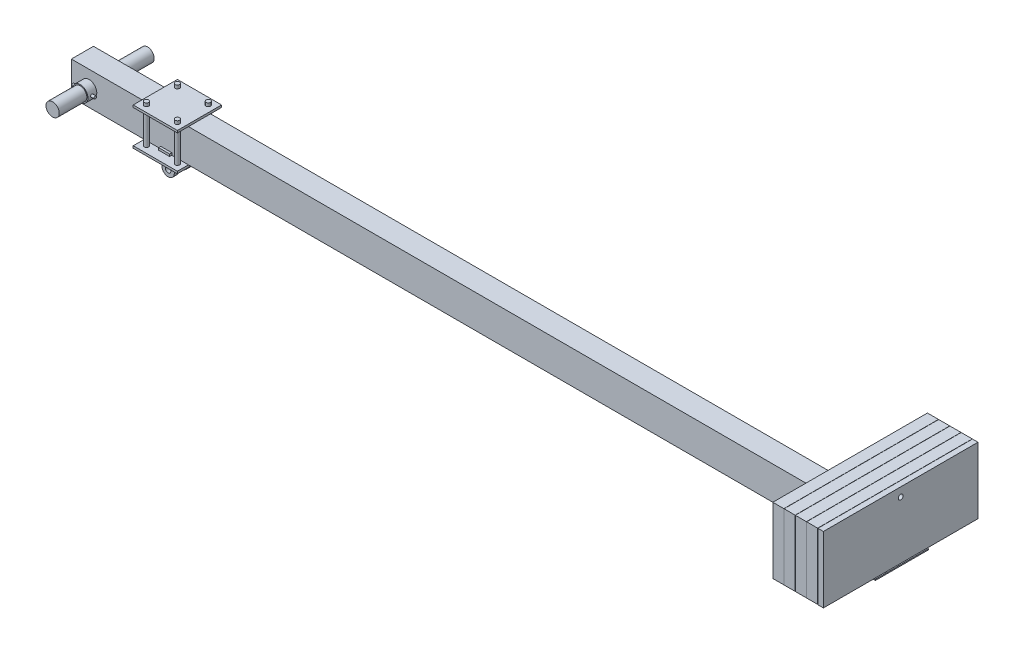
SolidWorks part; units mm, degrees
material "Plain Carbon Steel"
ref_plane "Front Plane" through (0, 0, 0) normal (0, 0, 1) x (1, 0, 0)
ref_plane "Top Plane" through (0, 0, 0) normal (0, 1, 0) x (1, 0, 0)
ref_plane "Right Plane" through (0, 0, 0) normal (1, 0, 0) x (0, 0, -1)
sketch "Sketch1" plane through (0, 0, 0) normal (0, 0, 1) x (1, 0, 0)
  line L0 (3600, 0) -> (0, 0) construction
  line L1 (0, -75) -> (3600, -75)
  line L2 (0, -75) -> (0, 75) construction
  line L3 (0, 75) -> (3600, 75)
  line L4 (3600, -75) -> (3600, 75) construction
  line L5 (3600, 225) -> (3600, -75) construction
  line L6 (3600, 75) -> (3600, 225)
  line L7 (3600, 225) -> (3650, 225)
  line L8 (3650, 225) -> (3650, -75)
  line L9 (3650, -75) -> (3600, -75)
  line L11 (3650, 225) -> (3651, 225) construction
  line L26 (0, 75) -> (-80, 75)
  line L27 (-80, 75) -> (-80, -75)
  line L28 (-80, -75) -> (0, -75)
  dimension "D1" = 3600
  dimension "D2" = 150
  dimension "D3" = 300
  dimension "D4" = 50
  dimension "D6" = 80
extrude "Boss-Extrude1" add sketch "Sketch1" along normal mid plane 100
sketch "Sketch2" plane through (0, 0, 0) normal (0, 0, 1) x (1, 0, 0)
  line L0 (-74, 0) -> (3600, 0) construction
  line L1 (-74, -69) -> (3600, -69)
  line L2 (-74, -69) -> (-74, 69)
  line L3 (-74, 69) -> (3600, 69)
  line L4 (3600, -69) -> (3600, 69)
  line L5 (3600, 75) -> (-80, 75) construction
  line L8 (3600, 225) -> (3600, 75) construction
  line L9 (-80, 75) -> (-80, -75) construction
  dimension "D1" = 6
  dimension "D2" = 6
extrude "Cut-Extrude1" cut sketch "Sketch2" against normal mid plane 88
sketch "Sketch3" plane through (0, 0, 0) normal (0, 0, 1) x (1, 0, 0)
  line L24 (3600, 225) -> (3600, 75) construction
  line L25 (3650, 225) -> (3600, 225) construction
  line L26 (3650, -75) -> (3650, 225) construction
  line L27 (-80, -75) -> (3650, -75) construction
  line L28 (3600, 225) -> (3600, -75)
  line L29 (3650, 225) -> (3600, 225)
  line L30 (3650, -75) -> (3650, 225)
  line L31 (3600, -75) -> (3650, -75)
extrude "Boss-Extrude2" add sketch "Sketch3" along normal mid plane 700
sketch "Sketch6" plane through (0, 0, 0) normal (0, 0, 1) x (1, 0, 0)
  line L0 (3600, 75) -> (-80, 75) construction
  line L1 (250, 75) -> (450, 75)
  line L2 (250, 75) -> (250, 85)
  line L3 (250, 85) -> (450, 85)
  line L4 (450, 75) -> (450, 85)
  line L5 (-80, -75) -> (3600, -75) construction
  line L6 (250, -75) -> (450, -75)
  line L7 (250, -75) -> (250, -85)
  line L8 (250, -85) -> (450, -85)
  line L9 (450, -75) -> (450, -85)
  line L10 (350, 85) -> (350, 75) construction
  dimension "D1" = 200
  dimension "D2" = 10
  dimension "D3" = 350
extrude "Boss-Extrude4" add sketch "Sketch6" along normal mid plane 200
sketch "Sketch14" plane through (0, 0, 0) normal (0, 0, 1) x (1, 0, 0)
  circle A0 centre (0, 0) radius 35
  dimension "D1" = 70
extrude "Cut-Extrude5" cut sketch "Sketch14" against normal mid plane 192
sketch "Sketch15" plane through (0, 0, 0) normal (0, 0, 1) x (1, 0, 0)
  circle A0 centre (0, 0) radius 30
  circle A1 centre (0, 0) radius 35
  dimension "D1" = 70
  dimension "D2" = 60
extrude "Boss-Extrude9" add sketch "Sketch15" along normal mid plane 180
sketch "Sketch8" plane through (0, 0, 0) normal (0, 0, 1) x (1, 0, 0)
  circle A0 centre (0, 0) radius 30
  dimension "D1" = 60
extrude "Boss-Extrude6" add sketch "Sketch8" along normal mid plane 430
sketch "Sketch9" plane through (0, 0, 0) normal (0, 0, 1) x (1, 0, 0)
  line L0 (250, -85) -> (450, -85) construction
  line L1 (250, -85) -> (450, -85) construction
  line L2 (350, -85) -> (350, 31.3926) construction
  line L3 (295, -85) -> (295, -110)
  line L4 (295, -110) -> (405, -110) construction
  line L5 (405, -85) -> (405, -110)
  line L6 (350, -110) -> (350, -309.6124) construction
  line L7 (378, -110) -> (378, -148)
  line L8 (322, -110) -> (322, -148)
  line L9 (295, -110) -> (322, -110)
  line L10 (378, -110) -> (405, -110)
  line L11 (295, -85) -> (405, -85)
  arc A0 (378, -148) -> (322, -148) centre (350, -148) cw
  circle A1 centre (350, -148) radius 12.5
  dimension "D3" = 28
  dimension "D4" = 25
  dimension "D1" = 25
  dimension "D2" = 110
  dimension "D5" = 38
extrude "Boss-Extrude7" add sketch "Sketch9" along normal mid plane 84
sketch "Sketch10" plane through (322, 0, 0) normal (-1, 0, 0) x (0, 0, 1)
  line L1 (-20, -85) -> (20, -85)
  line L2 (-20, -85) -> (-20, -176)
  line L3 (-20, -176) -> (20, -176)
  line L4 (20, -85) -> (20, -176)
  line L5 (-42, -176) -> (42, -176) construction
  line L6 (42, -85) -> (-42, -85) construction
  line L7 (-42, -129) -> (-20, -129) construction
  line L8 (-42, -110) -> (-42, -148) construction
  line L9 (20, -129) -> (42, -129) construction
  line L10 (42, -110) -> (42, -148) construction
  dimension "D1" = 40
extrude "Cut-Extrude3" cut sketch "Sketch10" against normal blind 170 and the other way blind 84
sketch "Sketch11" plane through (0, 0, 0) normal (0, 1, 0) x (1, 0, 0)
  line L0 (280, -70) -> (420, -70) construction
  line L1 (280, -70) -> (280, 70) construction
  line L2 (420, -70) -> (420, 70) construction
  line L3 (280, 70) -> (420, 70) construction
  line L4 (280, -70) -> (420, 70) construction
  line L5 (420, -70) -> (280, 70) construction
  line L6 (250, -100) -> (250, 100) construction
  line L7 (450, 100) -> (250, 100) construction
  line L8 (280, 0) -> (250, 0) construction
  line L9 (420, 0) -> (450, 0) construction
  line L10 (450, -100) -> (450, 100) construction
  circle A0 centre (420, 70) radius 10
  circle A1 centre (420, -70) radius 10
  circle A2 centre (280, -70) radius 10
  circle A3 centre (280, 70) radius 10
  point P1 (350, 0)
  dimension "D3" = 20
  dimension "D1" = 30
  dimension "D2" = 30
extrude "Boss-Extrude8" add sketch "Sketch11" along normal blind 100 and the other way blind 100
sketch "Sketch24" plane through (0, 75, 0) normal (0, 1, 0) x (1, 0, 0)
  line L0 (250, -50) -> (450, -50) construction
  line L1 (250, -50) -> (450, -50) construction
  line L2 (350, -50) -> (350, -158.2957) construction
  line L3 (325, -50) -> (375, -50)
  line L4 (325, -50) -> (325, -60)
  line L5 (325, -60) -> (375, -60)
  line L6 (375, -50) -> (375, -60)
  line L7 (0, 0) -> (647.6373, 0) construction
  line L8 (375, 50) -> (375, 60)
  line L9 (325, 60) -> (375, 60)
  line L10 (325, 50) -> (325, 60)
  line L11 (325, 50) -> (375, 50)
  point P8 (350, -50)
  point P9 (350, -60)
  dimension "D1" = 10
  dimension "D2" = 50
extrude "Boss-Extrude15" add sketch "Sketch24" against normal blind 10
sketch "Sketch25" plane through (0, -75, 0) normal (0, 1, 0) x (1, 0, 0)
  line L8 (325, -60) -> (325, -50) construction
  line L9 (325, -50) -> (375, -50) construction
  line L10 (375, -50) -> (375, -60) construction
  line L11 (375, -60) -> (325, -60) construction
  line L12 (375, 50) -> (325, 50) construction
  line L13 (325, 50) -> (325, 60) construction
  line L14 (325, 60) -> (375, 60) construction
  line L15 (375, 60) -> (375, 50) construction
  line L16 (325, -60) -> (325, -50)
  line L17 (325, -50) -> (375, -50)
  line L18 (375, -50) -> (375, -60)
  line L19 (375, -60) -> (325, -60)
  line L20 (375, 50) -> (325, 50)
  line L21 (325, 50) -> (325, 60)
  line L22 (325, 60) -> (375, 60)
  line L23 (375, 60) -> (375, 50)
extrude "Boss-Extrude16" add sketch "Sketch25" along normal blind 10
sketch "Sketch16" plane through (0, -75, 0) normal (0, -1, 0) x (1, 0, 0)
  line L0 (3250, -120) -> (3630, -120)
  line L1 (3250, -120) -> (3250, 120)
  line L2 (3630, -120) -> (3630, 120)
  line L3 (3250, 120) -> (3630, 120)
  line L4 (3250, -120) -> (3630, 120) construction
  line L5 (3630, -120) -> (3250, 120) construction
  line L6 (3650, 350) -> (3650, -350) construction
  line L7 (450, 50) -> (3600, 50) construction
  line L8 (450, -50) -> (3600, -50) construction
  line L9 (3600, 350) -> (3600, 50) construction
  point P1 (3440, 0)
  dimension "D1" = 20
  dimension "D2" = 70
  dimension "D3" = 70
  dimension "D4" = 350
extrude "Boss-Extrude10" add sketch "Sketch16" along normal blind 5
sketch "Sketch17" plane through (3600, 0, 0) normal (-1, 0, 0) x (0, 0, 1)
  line L0 (-350, 225) -> (-350, -75) construction
  line L2 (350, 225) -> (-350, 225) construction
  line B0 (0, -6.4214) -> (0, 225) construction
  line B1 (0, -6.4214) -> (319.7322, -6.4214) construction
  line B2 (350, 225) -> (-350, 225)
  line B3 (-350, 225) -> (-350, -74)
  line B4 (-350, -74) -> (-65, -74)
  line B5 (-65, -74) -> (-55, -64)
  line B6 (-55, 75.1) -> (55, 75.1)
  line B7 (-55, -64) -> (-55, 75.1)
  line B8 (55, -64) -> (55, 75.1)
  line B9 (65, -74) -> (55, -64)
  line B10 (350, -74) -> (65, -74)
  line B11 (350, 225) -> (350, -74)
sketch_block_instance "Block1-1"
sketch_block "Block1" parameters "D1"=135, "D2"=10, "D3"=230, "D4"=230, "D5"=285
extrude "Boss-Extrude11" add sketch "Sketch17" along normal blind 50 from offset 1 separate body
sketch "Sketch18" plane through (3549, 0, 0) normal (-1, 0, 0) x (0, 0, 1)
  line L0 (350, -74) -> (350, 225) construction
  line L1 (350, 225) -> (-350, 225) construction
  line B0 (350, 225) -> (-350, 225)
  line B1 (-350, 225) -> (-350, -74)
  line B2 (-350, -74) -> (-65, -74)
  line B3 (-65, -74) -> (-55, -64)
  line B4 (-55, 75.1) -> (55, 75.1)
  line B5 (-55, -64) -> (-55, 75.1)
  line B6 (55, -64) -> (55, 75.1)
  line B7 (65, -74) -> (55, -64)
  line B8 (350, -74) -> (65, -74)
  line B9 (350, 225) -> (350, -74)
sketch_block_instance "Block1-2"
extrude "Boss-Extrude12" add sketch "Sketch18" along normal blind 50 from offset 1 separate body
sketch "Sketch19" plane through (3498, 0, 0) normal (-1, 0, 0) x (0, 0, 1)
  line L0 (-350, 225) -> (-350, -74) construction
  line L1 (350, 225) -> (-350, 225) construction
  line B0 (350, 225) -> (-350, 225)
  line B1 (-350, 225) -> (-350, -74)
  line B2 (-350, -74) -> (-65, -74)
  line B3 (-65, -74) -> (-55, -64)
  line B4 (-55, 75.1) -> (55, 75.1)
  line B5 (-55, -64) -> (-55, 75.1)
  line B6 (55, -64) -> (55, 75.1)
  line B7 (65, -74) -> (55, -64)
  line B8 (350, -74) -> (65, -74)
  line B9 (350, 225) -> (350, -74)
sketch_block_instance "Block1-4"
extrude "Boss-Extrude13" add sketch "Sketch19" along normal blind 50 from offset 1 separate body
sketch "Sketch20" plane through (3447, 0, 0) normal (-1, 0, 0) x (0, 0, 1)
  line L0 (350, 225) -> (-350, 225) construction
  line L1 (350, -74) -> (350, 225) construction
  line B0 (350, 225) -> (-350, 225)
  line B1 (-350, 225) -> (-350, -74)
  line B2 (-350, -74) -> (-65, -74)
  line B3 (-65, -74) -> (-55, -64)
  line B4 (-55, 75.1) -> (55, 75.1)
  line B5 (-55, -64) -> (-55, 75.1)
  line B6 (55, -64) -> (55, 75.1)
  line B7 (65, -74) -> (55, -64)
  line B8 (350, -74) -> (65, -74)
  line B9 (350, 225) -> (350, -74)
sketch_block_instance "Block1-6"
extrude "Boss-Extrude14" add sketch "Sketch20" along normal blind 50 from offset 1 separate body
sketch "Sketch21" plane through (0, -80, 0) normal (0, -1, 0) x (1, 0, 0)
  line L0 (3250, 0) -> (3630, 0) construction
  line L1 (3630, -120) -> (3630, 120) construction
  line L2 (3250, 50) -> (3250, -50) construction
  line L3 (3290, 80) -> (3590, 80) construction
  line L4 (3290, 89) -> (3590, 89)
  line L5 (3290, 71) -> (3590, 71)
  line L6 (3650, 350) -> (3650, -350) construction
  line L7 (3250, 120) -> (3250, -120) construction
  line L8 (3290, -80) -> (3590, -80) construction
  line L9 (3290, -89) -> (3590, -89)
  line L10 (3290, -71) -> (3590, -71)
  arc A0 (3290, 89) -> (3290, 71) centre (3290, 80) ccw
  arc A1 (3590, 71) -> (3590, 89) centre (3590, 80) ccw
  arc A2 (3290, -89) -> (3290, -71) centre (3290, -80) cw
  arc A3 (3590, -71) -> (3590, -89) centre (3590, -80) cw
  point P8 (3440, 80)
  point P19 (3440, -80)
  dimension "D1" = 18
  dimension "D2" = 60
  dimension "D3" = 40
  dimension "D4" = 80
extrude "Cut-Extrude6" cut sketch "Sketch21" against normal up to surface (5 mm away) up to face at (3425, -75, 85)
sketch "Sketch22" plane through (0, -80, 0) normal (0, -1, 0) x (1, 0, 0)
  line L0 (3421, 350) -> (3421, -350) construction
  line L1 (3396, 350) -> (3446, 350) construction
  line L2 (3396, -350) -> (3446, -350) construction
  line L3 (3472, -350) -> (3472, 350) construction
  line L4 (3447, -350) -> (3497, -350) construction
  line L5 (3447, 350) -> (3497, 350) construction
  line L6 (3523, 350) -> (3523, -350) construction
  line L7 (3498, 350) -> (3548, 350) construction
  line L8 (3498, -350) -> (3548, -350) construction
  line L9 (3574, -350) -> (3574, 350) construction
  line L10 (3549, -350) -> (3599, -350) construction
  line L11 (3549, 350) -> (3599, 350) construction
  line L12 (3421, 80) -> (3574, 80) construction
  line L13 (3250, 0) -> (3630, 0) construction
  line L14 (3630, -120) -> (3630, 120) construction
  line L15 (3250, 120) -> (3250, -120) construction
  circle A0 centre (3421, 80) radius 8
  circle A1 centre (3472, 80) radius 8
  circle A2 centre (3523, 80) radius 8
  circle A3 centre (3574, 80) radius 8
  circle A4 centre (3574, -80) radius 8
  circle A5 centre (3523, -80) radius 8
  circle A6 centre (3472, -80) radius 8
  circle A7 centre (3421, -80) radius 8
  dimension "D2" = 16
  dimension "D1" = 80
extrude "Cut-Extrude7" cut sketch "Sketch22" against normal blind 30
sketch "Sketch23" plane through (3650, 0, 0) normal (1, 0, 0) x (0, 0, -1)
  line L0 (0, 0) -> (0, 225) construction
  line L1 (-350, 225) -> (350, 225) construction
  circle A0 centre (0, 185) radius 11
  dimension "D2" = 22
  dimension "D1" = 40
extrude "Cut-Extrude8" cut sketch "Sketch23" against normal up to surface (254 mm away) up to face at (3396, 17.62, 0)
sketch "Sketch26" plane through (3396, 0, 0) normal (-1, 0, 0) x (0, 0, 1)
  line L10 (-350, 225) -> (-350, -74)
  line L11 (-350, -74) -> (-65, -74)
  line L12 (-65, -74) -> (-55, -64)
  line L13 (-55, -64) -> (-55, 75.1)
  line L14 (-55, 75.1) -> (55, 75.1)
  line L15 (55, 75.1) -> (55, -64)
  line L16 (55, -64) -> (65, -74)
  line L17 (65, -74) -> (350, -74)
  line L18 (350, -74) -> (350, 225)
  line L19 (350, 225) -> (-350, 225)
  line L20 (-350, 225) -> (-350, -74)
  line L21 (-350, -74) -> (-65, -74)
  line L22 (-65, -74) -> (-55, -64)
  line L23 (-55, -64) -> (-55, 75.1)
  line L24 (-55, 75.1) -> (55, 75.1)
  line L25 (55, 75.1) -> (55, -64)
  line L26 (55, -64) -> (65, -74)
  line L27 (65, -74) -> (350, -74)
  line L28 (350, -74) -> (350, 225)
  line L29 (350, 225) -> (-350, 225)
  dimension "D1" = 0
extrude "Cut-Extrude9" [suppressed] cut sketch "Sketch26" against normal up to surface (204 mm away)
sketch "Sketch27" plane through (0, 75, 0) normal (0, 1, 0) x (1, 0, 0)
  line L0 (3600, 50) -> (450, 50) construction
  line L1 (3599.2561, 50) -> (3547.973, 50)
  line L2 (3599.2561, 50) -> (3599.2561, -50)
  line L3 (3599.2561, -50) -> (3547.973, -50)
  line L4 (3547.973, 50) -> (3547.973, -50)
  line L5 (3600, -50) -> (450, -50) construction
  line L7 (3546.5878, 50) -> (3497.0658, 50)
  line L8 (3546.5878, 50) -> (3546.5878, -50)
  line L9 (3546.5878, -50) -> (3497.0658, -50)
  line L10 (3497.0658, 50) -> (3497.0658, -50)
  line L11 (3495.8537, 50) -> (3446.0845, 50)
  line L12 (3495.8537, 50) -> (3495.8537, -50)
  line L13 (3495.8537, -50) -> (3446.0845, -50)
  line L14 (3446.0845, 50) -> (3446.0845, -50)
  line L15 (3444.8877, 50) -> (3395.1343, 50)
  line L16 (3444.8877, 50) -> (3444.8877, -50)
  line L17 (3444.8877, -50) -> (3395.1343, -50)
  line L18 (3395.1343, 50) -> (3395.1343, -50)
split line "Split Line1" [suppressed]
sketch "Sketch28" plane through (0, 0, 0) normal (1, 0, 0) x (0, 0, -1)
  line L0 (0, 0) -> (-116.4794, 0) construction
  line L1 (385, 0) -> (-385, 0) construction
  line L2 (-90, 30) -> (-90, -30) construction
  line L3 (0, 0) -> (0, 75) construction
  line L4 (-50, 75) -> (50, 75) construction
  circle A0 centre (-72, 0) radius 6
  circle A1 centre (72, 0) radius 6
  dimension "D1" = 12
  dimension "D2" = 18
extrude "Boss-Extrude17" add sketch "Sketch28" along normal mid plane 100
sketch "Sketch29" plane through (3650, 0, 0) normal (1, 0, 0) x (0, 0, -1)
  line L1 (-350, 225) -> (350, 225)
  line L2 (-350, 225) -> (-350, -75)
  line L3 (-350, -75) -> (350, -75)
  line L4 (350, 225) -> (350, -75)
extrude "Cut-Extrude10" cut sketch "Sketch29" against normal blind 25
